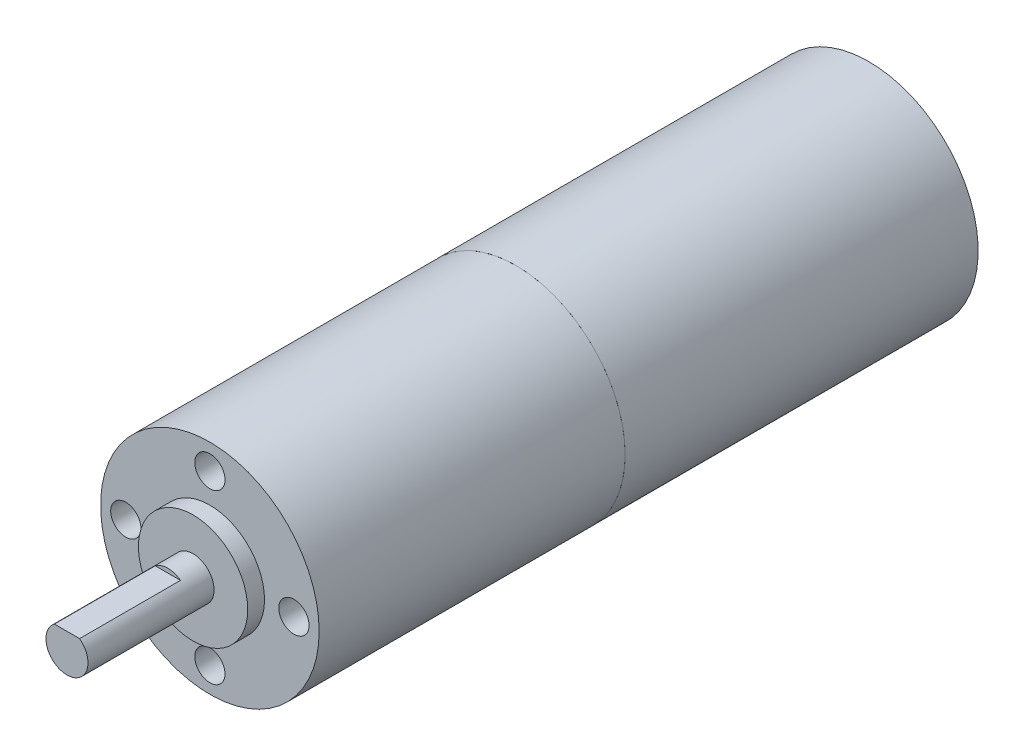
SolidWorks part; units mm, degrees
ref_plane "Plan de face" through (0, 0, 0) normal (0, 0, 1) x (1, 0, 0)
ref_plane "Plan de dessus" through (0, 0, 0) normal (0, 1, 0) x (1, 0, 0)
ref_plane "Plan de droite" through (0, 0, 0) normal (1, 0, 0) x (0, 0, -1)
sketch "Esquisse1" plane through (0, 0, 0) normal (0, 0, 1) x (1, 0, 0)
  circle A0 centre (0, 0) radius 13
  dimension "D1" = 26
extrude "Boss.-Extru. Reducteur" add sketch "Esquisse1" along normal blind 36.4
sketch "Esquisse2" plane through (0, 0, 36.4) normal (0, 0, 1) x (1, 0, 0)
  circle A0 centre (0, 0) radius 2.5
  dimension "D1" = 5
extrude "Boss.-Extru. Arbre" add sketch "Esquisse2" along normal blind 17
sketch "Esquisse4" plane through (0, 0, 36.4) normal (0, 0, 1) x (1, 0, 0)
  circle A0 centre (0, 0) radius 6.5
  circle A1 centre (0, 0) radius 2.5
extrude "Boss.-Extru.3" add sketch "Esquisse4" along normal blind 2
sketch "Esquisse5" plane through (0, 0, 36.4) normal (0, 0, 1) x (1, 0, 0)
  line L0 (0, 0) -> (10, 0) construction
  line L1 (0, 0) -> (0, 10) construction
  line L2 (0, 0) -> (-10, 0) construction
  line L3 (0, 0) -> (0, -10) construction
  circle A0 centre (0, 10) radius 1.8
  circle A1 centre (-10, 0) radius 1.8
  circle A2 centre (0, -10) radius 1.8
  circle A3 centre (10, 0) radius 1.8
extrude "Enlèv. mat.-Extru.2" cut sketch "Esquisse5" against normal blind 4
sketch "Esquisse6" plane through (0, 0, 53.4) normal (0, 0, 1) x (1, 0, 0)
  line L0 (0, -2.5) -> (0, 2) construction
  line L1 (0, 2) -> (1.5, 2)
  line L2 (0, 2) -> (-1.5, 2)
  circle A2 centre (0, 0) radius 2.5 construction
  circle A3 centre (0, 0) radius 2.5 construction
  arc A4 (-1.5, 2) -> (1.5, 2) centre (0, 0) cw
extrude "Enlèv. mat.-Extru.3" cut sketch "Esquisse6" against normal blind 12
sketch "Esquisse7" plane through (0, 0, 36.4) normal (0, 0, 1) x (1, 0, 0)
  circle A0 centre (0, 0) radius 2.4968
extrude "Boss.-Extru.4" add sketch "Esquisse7" along normal blind 3 separate body
sketch "Esquisse8" plane through (0, 0, 39.4) normal (0, 0, 1) x (1, 0, 0)
  circle A0 centre (0, 0) radius 2.5
sketch "Esquisse9" plane through (0, 0, 0) normal (0, 0, -1) x (-1, 0, 0)
  circle A0 centre (0, 0) radius 13
  dimension "D1" = 26
extrude "Boss.-Extru.5" add sketch "Esquisse9" along normal blind 42 separate body
